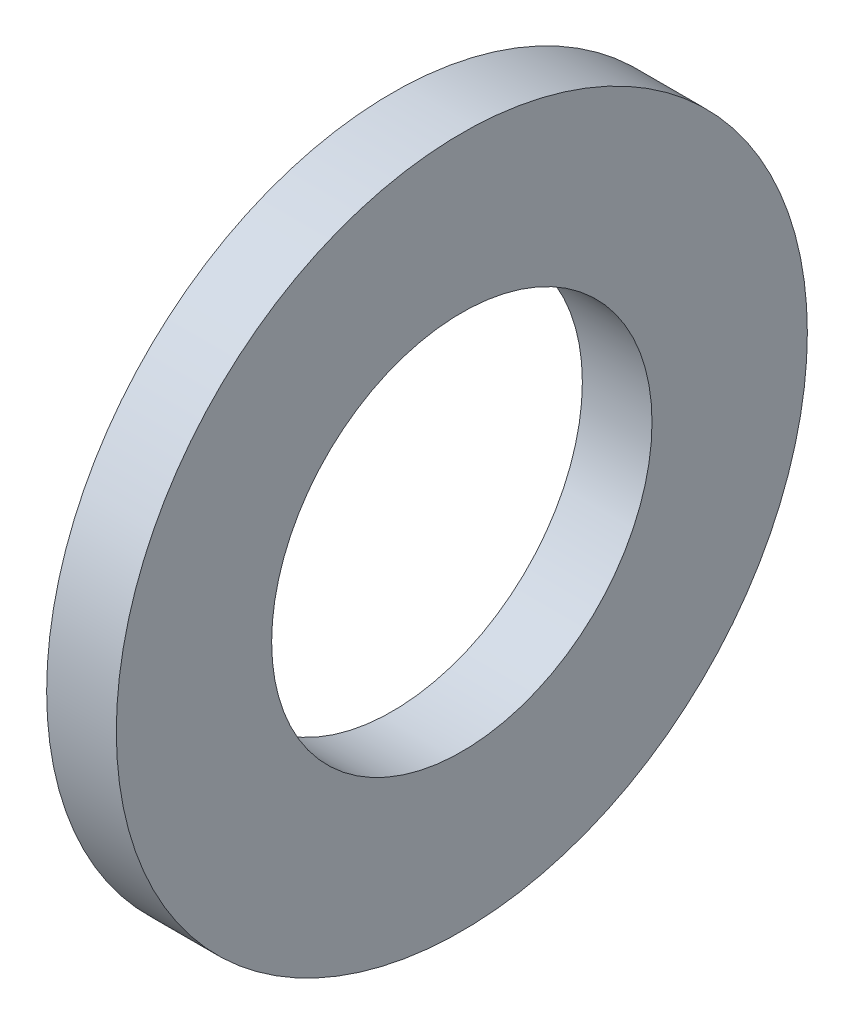
SolidWorks part; units mm, degrees
ref_plane "Plane1" through (0, 0, 0) normal (0, 0, 1) x (1, 0, 0)
ref_plane "Plane2" through (0, 0, 0) normal (0, 1, 0) x (1, 0, 0)
ref_plane "Plane3" through (0, 0, 0) normal (1, 0, 0) x (0, 0, -1)
sketch "Sketch1" plane through (0, 0, 0) normal (0, 0, 1) x (1, 0, 0)
  line L0 (-34.925, 0) -> (9.525, 0) construction
  line L1 (0, 4.3688) -> (0, 7.9375)
  line L2 (0, 7.9375) -> (-1.6002, 7.9375)
  line L3 (-1.6002, 7.9375) -> (-1.6002, 4.3688)
  line L4 (-1.6002, 4.3688) -> (0, 4.3688)
  dimension "Thickness" = 1.6002
  dimension "Inside_dia" = 8.7376
  dimension "Outside_dia" = 15.875
revolve "Base-Revolve" add sketch "Sketch1" angle 360 about L0
